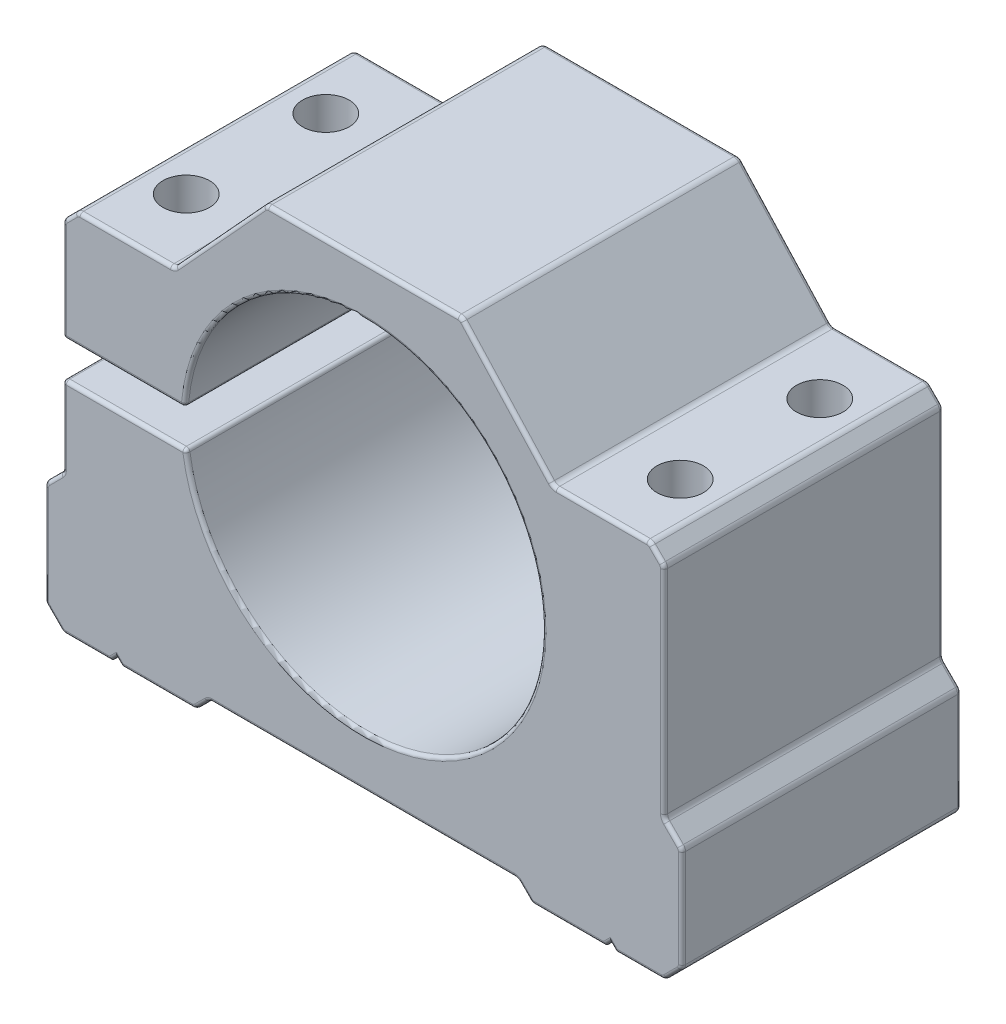
SolidWorks part; units mm, degrees
ref_plane "Спереди" through (0, 0, 0) normal (0, 0, 1) x (1, 0, 0)
ref_plane "Сверху" through (0, 0, 0) normal (0, 1, 0) x (1, 0, 0)
ref_plane "Справа" through (0, 0, 0) normal (1, 0, 0) x (0, 0, -1)
sketch "Эскиз1" plane through (0, 0, 0) normal (0, 0, 1) x (1, 0, 0)
  line L0 (0, 0) -> (0, -34) construction
  line L1 (104.0457, 305.8288) -> (697.3791, 305.8288) construction
  line L2 (-74.0406, 18) -> (88.3925, 18) construction
  line L3 (21.5, -32) -> (-21.5, -32)
  line L4 (-21.5, -32) -> (-23.5, -34)
  line L5 (-23.5, -34) -> (-33.75, -34)
  line L6 (-33.75, -34) -> (-34.5, -33.25)
  line L7 (-34.5, -33.25) -> (-35.25, -34)
  line L8 (-35.25, -34) -> (-42, -34)
  line L9 (-42, -34) -> (-44.5, -31.5)
  line L10 (-44.5, -31.5) -> (-44.5, -17)
  line L11 (-44.5, -17) -> (-42, -14.5)
  line L12 (-42, -14.5) -> (-42, 16)
  line L13 (-42, 16) -> (-40, 18)
  line L14 (-40, 18) -> (-26.5, 18)
  line L15 (-26.5, 18) -> (-13.6714, 32)
  line L16 (-13.6714, 32) -> (13.6714, 32)
  line L17 (0, 0) -> (-42, 0) construction
  line L18 (21.5, -32) -> (23.5, -34)
  line L19 (-42, -3.25) -> (-24.7878, -3.25)
  line L20 (-42, -3.25) -> (-42, 1.75)
  line L21 (-42, 1.75) -> (-24.7878, 1.75)
  line L22 (-24.7878, -3.25) -> (-24.7878, 1.75)
  line L23 (23.5, -34) -> (33.75, -34)
  line L24 (33.75, -34) -> (34.5, -33.25)
  line L25 (34.5, -33.25) -> (35.25, -34)
  line L26 (35.25, -34) -> (42, -34)
  line L27 (42, -34) -> (44.5, -31.5)
  line L28 (44.5, -31.5) -> (44.5, -17)
  line L29 (44.5, -17) -> (42, -14.5)
  line L30 (42, -14.5) -> (42, 16)
  line L31 (42, 16) -> (40, 18)
  line L32 (40, 18) -> (26.5, 18)
  line L33 (26.5, 18) -> (13.6714, 32)
  circle A0 centre (0, 0) radius 25
  point P28 (0, 0)
  point P30 (0, -32)
  point P42 (0, 32)
  dimension "D1" = 50
  dimension "D2" = 34
  dimension "D3" = 52
  dimension "D4" = 89
  dimension "D5" = 2
  dimension "D6" = 2.5
  dimension "D7" = 45
  dimension "D8" = 1.5
  dimension "D9" = 69
  dimension "D10" = 18.5
  dimension "D11" = 14.5
  dimension "D12" = 2.5
  dimension "D13" = 1.75
  dimension "D14" = 5
  dimension "D15" = 2
  dimension "D16" = 15.5
  dimension "D17" = 47.5
  dimension "D18" = 66
extrude "Бобышка-Вытянуть1" add sketch "Эскиз1" along normal mid plane 39 contours A0 L19 L12 L11 L10 L9 L8 L7 L6 L5 L4 L3 L18 L23 L24 L25 L26 L27 L28 L29 L30 L31 L32 L33 L16 L15 L14 L13 L21
sketch "Эскиз2" plane through (0, 18, 0) normal (0, 1, 0) x (1, 0, 0)
  line L0 (34.5, -19.5) -> (34.5, 19.5) construction
  line L1 (-34.5, -9.75) -> (34.5, -9.75) construction
  line L2 (-34.5, -9.75) -> (-34.5, 9.75) construction
  line L3 (-34.5, 9.75) -> (34.5, 9.75) construction
  line L4 (34.5, -9.75) -> (34.5, 9.75) construction
  line L5 (-34.5, -9.75) -> (34.5, 9.75) construction
  line L6 (-34.5, 9.75) -> (34.5, -9.75) construction
  line L7 (0, 19.5) -> (0, 9.75) construction
  line L8 (21.5, 19.5) -> (-21.5, 19.5) construction
  line L9 (0, 9.75) -> (0, 0) construction
  line L10 (0, 0) -> (0, -9.75) construction
  line L11 (0, -9.75) -> (0, -19.5) construction
  line L12 (21.5, -19.5) -> (-21.5, -19.5) construction
  circle A0 centre (-34.5, -9.75) radius 3.25
  circle A1 centre (-34.5, 9.75) radius 3.25
  circle A2 centre (34.5, -9.75) radius 3.25
  circle A3 centre (34.5, 9.75) radius 3.25
  point P0 (0, 0)
  dimension "D1" = 6.5
extrude "Вырез-Вытянуть1" cut sketch "Эскиз2" against normal through all
fillet "Скругление1" radius 1 20 edges at (-42, 16, 0) (-40, 18, 0) (-26.5, 18, 0) (-13.6714, 32, 0) (26.5, 18, 0) (13.6714, 32, 0) (40, 18, 0) (42, 16, 0) (42, -14.5, 0) (44.5, -17, 0) (44.5, -31.5, 0) (42, -34, 0) (23.5, -34, 0) (21.5, -32, 0) (-21.5, -32, 0) (-23.5, -34, 0) (-42, -34, 0) (-44.5, -31.5, 0) (-42, -14.5, 0) (-44.5, -17, 0)
fillet "Скругление2" radius 0.5 104 edges at (-39.9685, 17.9239, 19.5) (-33.2629, 18, 19.5) (-26.5373, 18.0847, 19.5) (-20.0857, 25, 19.5) (-13.6341, 31.9153, 19.5) (0, 32, 19.5) (13.6341, 31.9153, 19.5) (20.0857, 25, 19.5) (26.5373, 18.0847, 19.5) (33.2629, 18, 19.5) (39.9685, 17.9239, 19.5) (41, 17, 19.5) (41.9239, 15.9685, 19.5) (42, 0.75, 19.5) (42.0761, -14.4685, 19.5) (43.25, -15.75, 19.5) (44.4239, -17.0315, 19.5) (44.5, -24.25, 19.5) (44.4239, -31.4685, 19.5) (43.25, -32.75, 19.5) (41.9685, -33.9239, 19.5) (38.4179, -34, 19.5) (34.875, -33.625, 19.5) (34.125, -33.625, 19.5) (28.8321, -34, 19.5) (23.5315, -33.9239, 19.5) (22.5, -33, 19.5) (21.4685, -32.0761, 19.5) (0, -32, 19.5) (-21.4685, -32.0761, 19.5) (-22.5, -33, 19.5) (-23.5315, -33.9239, 19.5) (-28.8321, -34, 19.5) (-34.125, -33.625, 19.5) (-34.875, -33.625, 19.5) (-38.4179, -34, 19.5) (-41.9685, -33.9239, 19.5) (-43.25, -32.75, 19.5) (-44.4239, -31.4685, 19.5) (-44.5, -24.25, 19.5) (-44.4239, -17.0315, 19.5) (-43.25, -15.75, 19.5) (-42.0761, -14.4685, 19.5) (-42, -8.6679, 19.5) (-33.3939, -3.25, 19.5) (24.9886, 0.7538, 19.5) (-33.4693, 1.75, 19.5) (-42, 8.6679, 19.5) (-41.9239, 15.9685, 19.5) (-41, 17, 19.5) (-24.9387, 1.75, 0) (-24.7878, -3.25, 0) (-33.4693, 1.75, -19.5) (24.9886, 0.7538, -19.5) (-33.3939, -3.25, -19.5) (-42, -8.6679, -19.5) (-42.0761, -14.4685, -19.5) (-43.25, -15.75, -19.5) (-44.4239, -17.0315, -19.5) (-44.5, -24.25, -19.5) (-44.4239, -31.4685, -19.5) (-43.25, -32.75, -19.5) (-41.9685, -33.9239, -19.5) (-38.4179, -34, -19.5) (-34.875, -33.625, -19.5) (-34.125, -33.625, -19.5) (-28.8321, -34, -19.5) (-23.5315, -33.9239, -19.5) (-22.5, -33, -19.5) (-21.4685, -32.0761, -19.5) (0, -32, -19.5) (21.4685, -32.0761, -19.5) (22.5, -33, -19.5) (23.5315, -33.9239, -19.5) (28.8321, -34, -19.5) (34.125, -33.625, -19.5) (34.875, -33.625, -19.5) (38.4179, -34, -19.5) (41.9685, -33.9239, -19.5) (43.25, -32.75, -19.5) (44.4239, -31.4685, -19.5) (44.5, -24.25, -19.5) (44.4239, -17.0315, -19.5) (43.25, -15.75, -19.5) (42.0761, -14.4685, -19.5) (42, 0.75, -19.5) (41.9239, 15.9685, -19.5) (41, 17, -19.5) (39.9685, 17.9239, -19.5) (33.2629, 18, -19.5) (26.5373, 18.0847, -19.5) (20.0857, 25, -19.5) (13.6341, 31.9153, -19.5) (0, 32, -19.5) (-13.6341, 31.9153, -19.5) (-20.0857, 25, -19.5) (-26.5373, 18.0847, -19.5) (-33.2629, 18, -19.5) (-39.9685, 17.9239, -19.5) (-41, 17, -19.5) (-41.9239, 15.9685, -19.5) (-42, 8.6679, -19.5) (-42, 1.75, 0) (-42, -3.25, 0)
